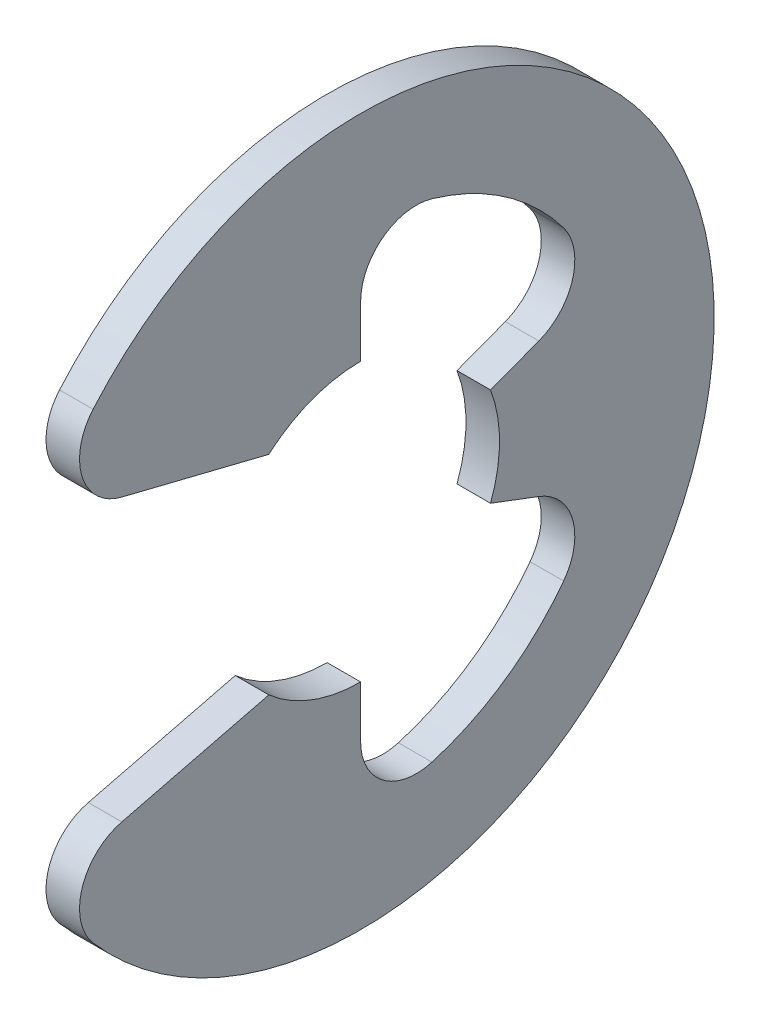
SolidWorks part; units mm, degrees
material "Cast Carbon Steel"
ref_plane "Front" through (0, 0, 0) normal (0, 0, 1) x (1, 0, 0)
ref_plane "Top" through (0, 0, 0) normal (0, 1, 0) x (1, 0, 0)
ref_plane "Right" through (0, 0, 0) normal (1, 0, 0) x (0, 0, -1)
sketch "Sketch1" plane through (0, 0, 0) normal (1, 0, 0) x (0, 0, -1)
  line L0 (-5.9715, -3.0225) -> (-1.7389, -1.9717)
  line L1 (-5.9715, 3.0225) -> (-1.7389, 1.9717)
  line L2 (0, -2.6289) -> (0, -4.8113)
  line L3 (0, 2.6289) -> (0, 4.8113)
  line L4 (2.4591, -0.9295) -> (4.5005, -1.701)
  line L5 (2.4591, 0.9295) -> (4.5005, 1.701)
  line L6 (0, 0) -> (-6.858, 0) construction
  line L7 (2.4591, 0.9295) -> (2.4591, -0.9295) construction
  line L8 (0, -2.6289) -> (-1.7389, -1.9717) construction
  circle A1 centre (0, 0) radius 6.858 construction
  circle A2 centre (0, 0) radius 2.6289 construction
  arc A3 (-5.9715, -3.0225) -> (-5.9715, 3.0225) centre (0, 0) ccw
  arc A4 (-1.7389, -1.9717) -> (0, -2.6289) centre (0, 0) ccw
  arc A5 (-1.7389, 1.9717) -> (0, 2.6289) centre (0, 0) cw
  arc A6 (2.4591, 0.9295) -> (2.4591, -0.9295) centre (0, 0) cw
  arc A7 (0, -4.8113) -> (4.5005, -1.701) centre (0, 0) ccw
  arc A8 (4.5005, 1.701) -> (0, 4.8113) centre (0, 0) ccw
  dimension "D1" = 4.8113
  dimension "OD" = 13.3858
  dimension "L" = 13.716
  dimension "D" = 5.2578
  dimension "D2" = 2.9892
  dimension "D3" = 3.9434
extrude "Extrude1" add sketch "Sketch1" along normal mid plane 0.635
fillet "Fillet1" radius 1.0541 6 edges at (0, -4.8113, 0) (0, 4.8113, 0) (0, -3.0225, 5.9715) (0, 3.0225, 5.9715) (0, -1.701, -4.5005) (0, 1.701, -4.5005)
sketch "Sketch3" plane through (0, 0, 0) normal (0, 1, 0) x (1, 0, 0)
  line L0 (0.3683, 3.175) -> (0.3683, 2.667)
  line L1 (0.3683, 2.667) -> (-0.3683, 2.667)
  line L2 (-0.3683, 2.667) -> (-0.3683, 3.175)
  line L3 (-0.3683, 3.175) -> (-7.9184, 3.175)
  line L4 (3.1306, 0) -> (3.1306, 2.921)
  line L5 (-7.9184, 3.175) -> (-7.9184, 0)
  line L6 (-7.9184, 0) -> (3.1306, 0)
  line L8 (3.1306, 0) -> (3.1306, 3.175) construction
  line L9 (3.1306, 3.175) -> (0.3683, 3.175) construction
  line L10 (3.1306, 0) -> (17.2631, 0) construction
  line L11 (3.1306, 2.921) -> (2.8765, 3.175)
  line L12 (2.8765, 3.175) -> (0.3683, 3.175)
  point P2 (0, 2.667)
  point P5 (0.3683, 2.921)
  dimension "D1" = 2.7622
  dimension "Ds" = 6.35
  dimension "Dg" = 5.334
  dimension "W" = 0.7366
  dimension "D2" = 11.049
  dimension "D3" = 45
revolve "Revolve2" [suppressed] add sketch "Sketch3" angle 360 about L10
equation "\"D2@Sketch3\" = \"W@Sketch3\"*15"
equation "\"D1@Sketch3\" = \"D2@Sketch3\"/4"
equation "\"D1@Sketch1\" = (\"OD@Sketch1\"+\"D@Sketch1\")/3.875"
equation "\"D3@Sketch1\" = \"D@Sketch1\"*.75"
